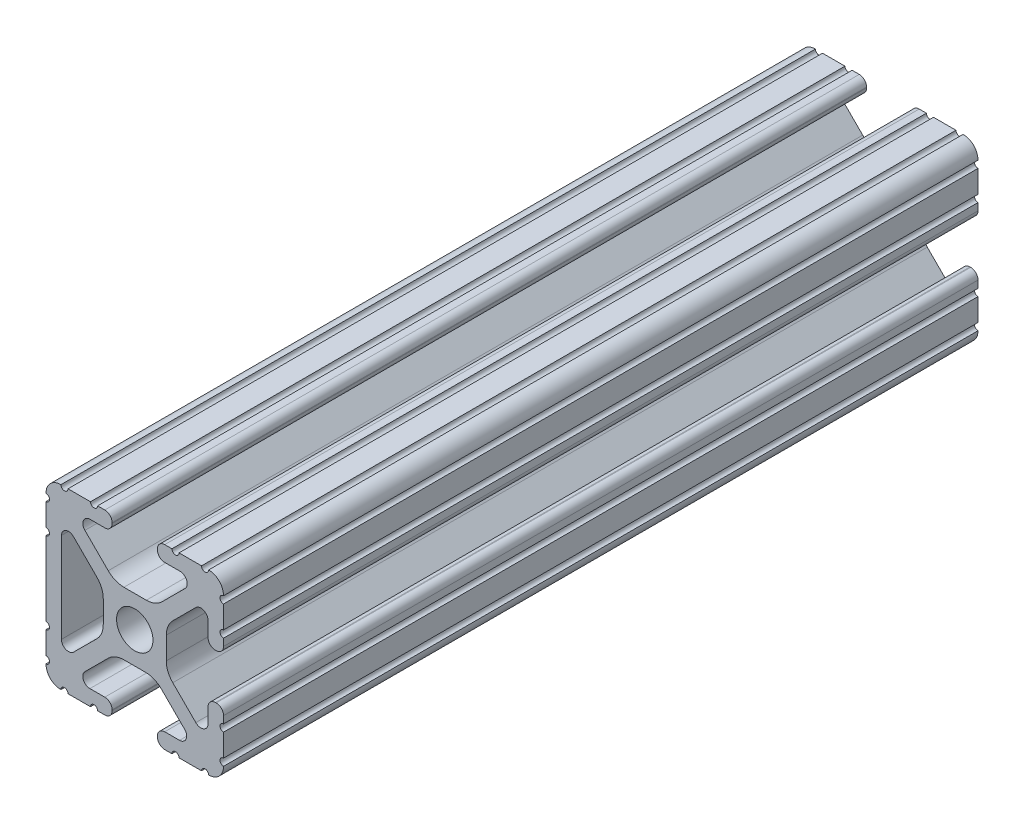
SolidWorks part; units mm, degrees
material "6061-T6 (SS)"
ref_plane "Front Plane" through (0, 0, 0) normal (0, 0, 1) x (1, 0, 0)
ref_plane "Top Plane" through (0, 0, 0) normal (0, 1, 0) x (1, 0, 0)
ref_plane "Right Plane" through (0, 0, 0) normal (1, 0, 0) x (0, 0, -1)
ref_plane "Plane1" through (0, 0, -152.4) normal (0, 0, -1) x (-1, 0, 0)
sketch "Sketch1" plane through (0, 0, -152.4) normal (0, 0, -1) x (-1, 0, 0)
  line L0 (6.4164, -10.4902) -> (4.2875, -10.4902)
  line L1 (3.2385, -11.5392) -> (3.2385, -11.651)
  line L2 (4.2875, -12.7) -> (5.3171, -12.7)
  line L3 (6.3331, -12.7) -> (9.5504, -12.7)
  line L4 (12.7, -9.5504) -> (12.7, -6.3331)
  line L5 (12.7, -5.3171) -> (12.7, 5.3171)
  line L6 (12.7, 6.3331) -> (12.7, 9.5504)
  line L7 (9.5504, 12.7) -> (6.3331, 12.7)
  line L8 (5.3171, 12.7) -> (4.2875, 12.7)
  line L9 (3.2384, 11.651) -> (3.2384, 11.5392)
  line L10 (4.2875, 10.4902) -> (6.4164, 10.4902)
  line L11 (7.1341, 8.7551) -> (3.7966, 5.4237)
  line L12 (1.5536, 4.4958) -> (-1.6573, 4.4958)
  line L13 (-3.9003, 5.4237) -> (-7.2072, 8.7245)
  line L14 (-6.4768, 10.4902) -> (-4.2875, 10.4902)
  line L15 (-3.2384, 11.5392) -> (-3.2384, 11.651)
  line L16 (-4.2875, 12.7) -> (-5.3171, 12.7)
  line L17 (-6.3331, 12.7) -> (-9.5504, 12.7)
  line L18 (-12.7, 9.5504) -> (-12.7, 6.3331)
  line L19 (-12.7, 5.3171) -> (-12.7, 4.2875)
  line L20 (-11.651, 3.2385) -> (-11.5392, 3.2385)
  line L21 (-10.4902, 4.2875) -> (-10.4902, 6.4021)
  line L22 (-8.737, 7.1292) -> (-5.4405, 3.8388)
  line L23 (-4.5085, 1.5917) -> (-4.5085, -1.5917)
  line L24 (-5.4405, -3.8388) -> (-8.737, -7.1292)
  line L25 (-10.4902, -6.4021) -> (-10.4902, -4.2875)
  line L26 (-11.5392, -3.2385) -> (-11.651, -3.2385)
  line L27 (-12.7, -4.2875) -> (-12.7, -5.3171)
  line L28 (-12.7, -6.3331) -> (-12.7, -9.5504)
  line L29 (-9.5504, -12.7) -> (-6.3331, -12.7)
  line L30 (-5.3171, -12.7) -> (-4.2875, -12.7)
  line L31 (-3.2385, -11.651) -> (-3.2385, -11.5392)
  line L32 (-4.2875, -10.4902) -> (-6.4083, -10.4902)
  line L33 (-7.1285, -8.7494) -> (-3.7967, -5.4237)
  line L34 (-1.5536, -4.4958) -> (1.5536, -4.4958)
  line L35 (3.7967, -5.4237) -> (7.1342, -8.7551)
  line L36 (10.4902, 6.4464) -> (10.4902, -6.4254)
  line L37 (8.7534, -7.1457) -> (5.4405, -3.8388)
  line L38 (4.5085, -1.5917) -> (4.5085, 1.5917)
  line L39 (5.4405, 3.8388) -> (8.7683, 7.1606)
  arc A0 (4.2875, -10.4902) -> (3.2385, -11.5392) centre (4.2875, -11.5392) ccw
  arc A1 (3.2385, -11.651) -> (4.2875, -12.7) centre (4.2875, -11.651) ccw
  arc A2 (5.3171, -12.7) -> (6.3331, -12.7) centre (5.8251, -12.7) cw
  arc A3 (9.5504, -12.7) -> (10.5664, -12.6998) centre (10.0584, -12.7) cw
  arc A4 (10.5664, -12.6998) -> (12.6998, -10.5664) centre (10.5918, -10.5918) ccw
  arc A5 (12.6998, -10.5664) -> (12.7, -9.5504) centre (12.7, -10.0584) cw
  arc A6 (12.7, -6.3331) -> (12.7, -5.3171) centre (12.7, -5.8251) cw
  arc A7 (12.7, 5.3171) -> (12.7, 6.3331) centre (12.7, 5.8251) cw
  arc A8 (12.7, 9.5504) -> (12.6998, 10.5664) centre (12.7, 10.0584) cw
  arc A9 (12.6998, 10.5664) -> (10.5664, 12.6998) centre (10.5918, 10.5918) ccw
  arc A10 (10.5664, 12.6998) -> (9.5504, 12.7) centre (10.0584, 12.7) cw
  arc A11 (6.3331, 12.7) -> (5.3171, 12.7) centre (5.8251, 12.7) cw
  arc A12 (4.2875, 12.7) -> (3.2384, 11.651) centre (4.2875, 11.651) ccw
  arc A13 (3.2384, 11.5392) -> (4.2875, 10.4902) centre (4.2875, 11.5392) ccw
  arc A14 (6.4164, 10.4902) -> (7.1341, 8.7551) centre (6.4164, 9.4742) cw
  arc A15 (3.7966, 5.4237) -> (1.5536, 4.4958) centre (1.5536, 7.6708) cw
  arc A16 (-1.6573, 4.4958) -> (-3.9003, 5.4237) centre (-1.6573, 7.6708) cw
  arc A17 (-7.2072, 8.7245) -> (-6.4768, 10.4902) centre (-6.4768, 9.4563) cw
  arc A18 (-4.2875, 10.4902) -> (-3.2384, 11.5392) centre (-4.2875, 11.5392) ccw
  arc A19 (-3.2384, 11.651) -> (-4.2875, 12.7) centre (-4.2875, 11.651) ccw
  arc A20 (-5.3171, 12.7) -> (-6.3331, 12.7) centre (-5.8251, 12.7) cw
  arc A21 (-9.5504, 12.7) -> (-10.5664, 12.6998) centre (-10.0584, 12.7) cw
  arc A22 (-10.5664, 12.6998) -> (-12.6998, 10.5664) centre (-10.5918, 10.5918) ccw
  arc A23 (-12.6998, 10.5664) -> (-12.7, 9.5504) centre (-12.7, 10.0584) cw
  arc A24 (-12.7, 6.3331) -> (-12.7, 5.3171) centre (-12.7, 5.8251) cw
  arc A25 (-12.7, 4.2875) -> (-11.651, 3.2385) centre (-11.651, 4.2875) ccw
  arc A26 (-11.5392, 3.2385) -> (-10.4902, 4.2875) centre (-11.5392, 4.2875) ccw
  arc A27 (-10.4902, 6.4021) -> (-8.737, 7.1292) centre (-9.4628, 6.4021) cw
  arc A28 (-5.4405, 3.8388) -> (-4.5085, 1.5917) centre (-7.6835, 1.5917) cw
  arc A29 (-4.5085, -1.5917) -> (-5.4405, -3.8388) centre (-7.6835, -1.5917) cw
  arc A30 (-8.737, -7.1292) -> (-10.4902, -6.4021) centre (-9.4628, -6.4021) cw
  arc A31 (-10.4902, -4.2875) -> (-11.5392, -3.2385) centre (-11.5392, -4.2875) ccw
  arc A32 (-11.651, -3.2385) -> (-12.7, -4.2875) centre (-11.651, -4.2875) ccw
  arc A33 (-12.7, -5.3171) -> (-12.7, -6.3331) centre (-12.7, -5.8251) cw
  arc A34 (-12.7, -9.5504) -> (-12.6998, -10.5664) centre (-12.7, -10.0584) cw
  arc A35 (-12.6998, -10.5664) -> (-10.5664, -12.6998) centre (-10.5918, -10.5918) ccw
  arc A36 (-10.5664, -12.6998) -> (-9.5504, -12.7) centre (-10.0584, -12.7) cw
  arc A37 (-6.3331, -12.7) -> (-5.3171, -12.7) centre (-5.8251, -12.7) cw
  arc A38 (-4.2875, -12.7) -> (-3.2385, -11.651) centre (-4.2875, -11.651) ccw
  arc A39 (-3.2385, -11.5392) -> (-4.2875, -10.4902) centre (-4.2875, -11.5392) ccw
  arc A40 (-6.4083, -10.4902) -> (-7.1285, -8.7494) centre (-6.4083, -9.4709) cw
  arc A41 (-3.7967, -5.4237) -> (-1.5536, -4.4958) centre (-1.5536, -7.6708) cw
  arc A42 (1.5536, -4.4958) -> (3.7967, -5.4237) centre (1.5536, -7.6708) cw
  arc A43 (7.1342, -8.7551) -> (6.4164, -10.4902) centre (6.4164, -9.4742) cw
  arc A44 (8.7683, 7.1606) -> (10.4902, 6.4464) centre (9.4812, 6.4464) cw
  arc A45 (10.4902, -6.4254) -> (8.7534, -7.1457) centre (9.4724, -6.4254) cw
  arc A46 (5.4405, -3.8388) -> (4.5085, -1.5917) centre (7.6835, -1.5917) cw
  arc A47 (4.5085, 1.5917) -> (5.4405, 3.8388) centre (7.6835, 1.5917) cw
  circle A48 centre (0, 0) radius 2.6035
extrude "Boss-Extrude1" add sketch "Sketch1" against normal blind 107.95
